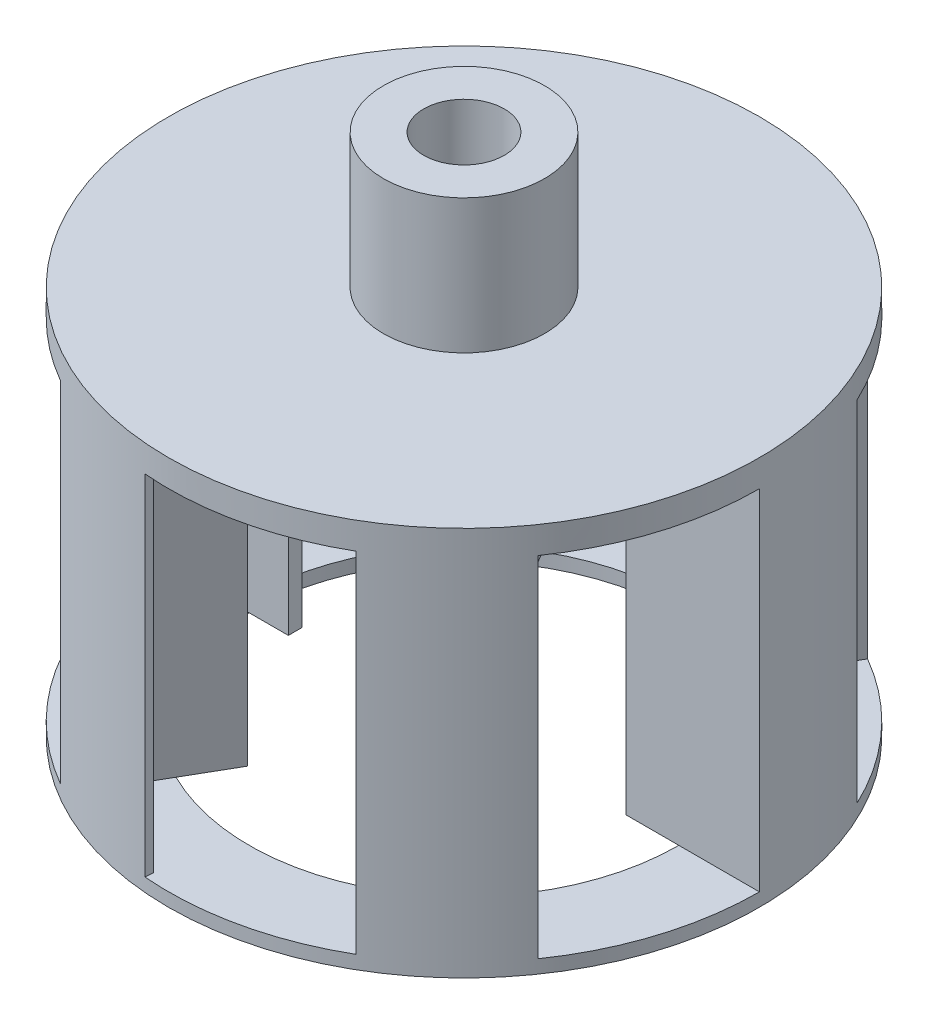
SolidWorks part; units mm, degrees
ref_plane "Front Plane" through (0, 0, 0) normal (0, 0, 1) x (1, 0, 0)
ref_plane "Top Plane" through (0, 0, 0) normal (0, 1, 0) x (1, 0, 0)
ref_plane "Right Plane" through (0, 0, 0) normal (1, 0, 0) x (0, 0, -1)
sketch "Sketch1" plane through (0, 0, 0) normal (0, 1, 0) x (1, 0, 0)
  circle A0 centre (0, 0) radius 5.5
  dimension "D1" = 11
extrude "Boss-Extrude1" add sketch "Sketch1" along normal blind 0.5
sketch "Sketch2" plane through (0, 0.5, 0) normal (0, 1, 0) x (1, 0, 0)
  circle A0 centre (0, 0) radius 1.5
  dimension "D2" = 3
extrude "Boss-Extrude2" add sketch "Sketch2" along normal blind 2.5
sketch "Sketch3" plane through (0, 0, 0) normal (0, -1, 0) x (1, 0, 0)
  line L0 (0, 0) -> (-6.04, 0) construction
  line L1 (-5.5, 0) -> (-3.02, 0)
  line L2 (-3.02, 0) -> (-3.02, 0.25)
  line L3 (-3.02, 0.25) -> (-5.3481, 0.25)
  line L4 (-4.9764, 2.3422) -> (-4.8442, 2.28)
  circle A0 centre (0, 0) radius 5.5 construction
  arc A1 (-4.8442, 2.28) -> (-5.3481, 0.25) centre (0, 0) ccw
  arc A2 (-5.5, 0) -> (-4.9764, 2.3422) centre (0, 0) cw
  dimension "D1" = 2.48
  dimension "D2" = 2.4
  dimension "D3" = 0.25
extrude "Boss-Extrude3" add sketch "Sketch3" along normal blind 6.5
pattern_circular "CirPattern1" count 6 over 360 about axis through (0, 0, 0) along (0, 1, 0) of "Boss-Extrude3"
sketch "Sketch4" plane through (0, -6.5, 0) normal (0, -1, 0) x (1, 0, 0)
  circle A0 centre (0, 0) radius 5.5
  circle A1 centre (0, 0) radius 4
  dimension "D1" = 8
  dimension "D2" = 11
extrude "Boss-Extrude4" add sketch "Sketch4" along normal blind 0.25
sketch "Sketch5" plane through (0, 3, 0) normal (0, 1, 0) x (1, 0, 0)
  circle A0 centre (0, 0) radius 0.75
  dimension "D1" = 1.5
extrude "Cut-Extrude1" cut sketch "Sketch5" against normal up to next
